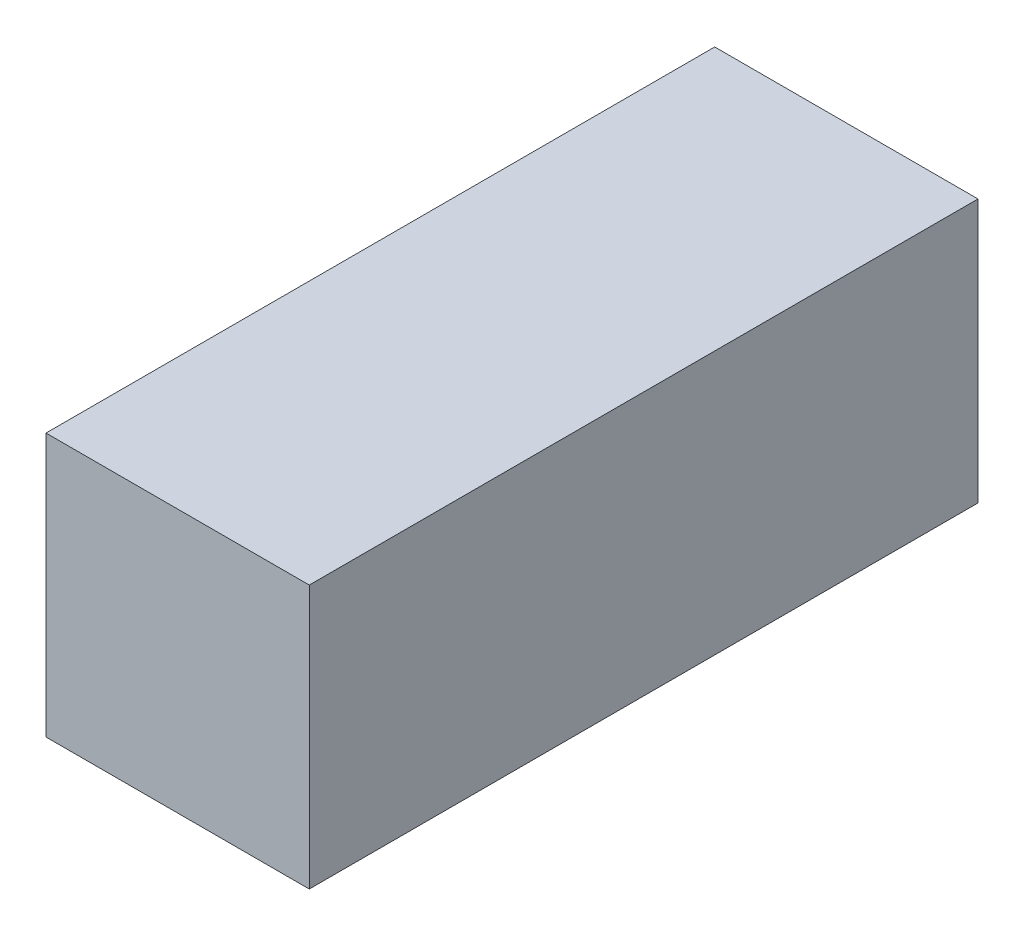
SolidWorks part; units mm, degrees
material "Teak"
ref_plane "Front Plane" through (0, 0, 0) normal (0, 0, 1) x (1, 0, 0)
ref_plane "Top Plane" through (0, 0, 0) normal (0, 1, 0) x (1, 0, 0)
ref_plane "Right Plane" through (0, 0, 0) normal (1, 0, 0) x (0, 0, -1)
sketch "Sketch1" plane through (0, 0, 0) normal (0, 0, 1) x (1, 0, 0)
  line L14 (0.0799, 0.0937) -> (0.0799, 5.0937)
  line L15 (0.0799, 0.0937) -> (5.0799, 0.0937)
  line L16 (5.0799, 0.0937) -> (5.0799, 5.0937)
  line L17 (0.0799, 5.0937) -> (5.0799, 5.0937)
extrude "Boss-Extrude1" add sketch "Sketch1" along normal blind 12.7
